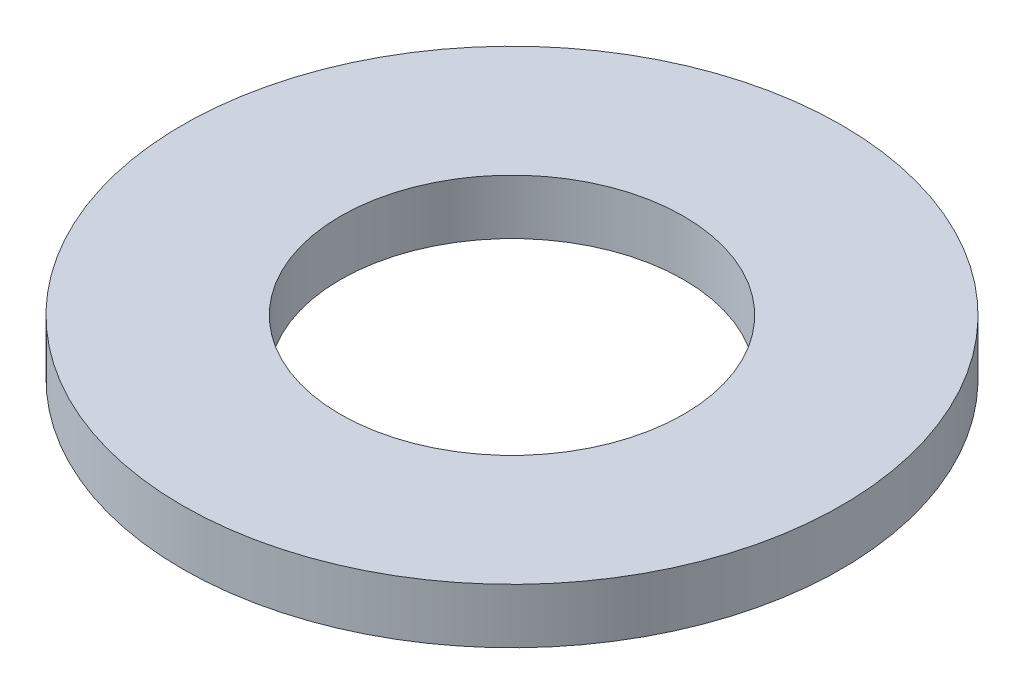
SolidWorks part; units mm, degrees
ref_plane "Front Plane" through (0, 0, 0) normal (0, 0, 1) x (1, 0, 0)
ref_plane "Top Plane" through (0, 0, 0) normal (0, 1, 0) x (1, 0, 0)
ref_plane "Right Plane" through (0, 0, 0) normal (1, 0, 0) x (0, 0, -1)
sketch "Sketch1" plane through (0, 0, 0) normal (0, 1, 0) x (1, 0, 0)
  circle A0 centre (0, 0) radius 3.125
  circle A1 centre (0, 0) radius 6
extrude "Boss-Extrude1" add sketch "Sketch1" along normal mid plane 1
